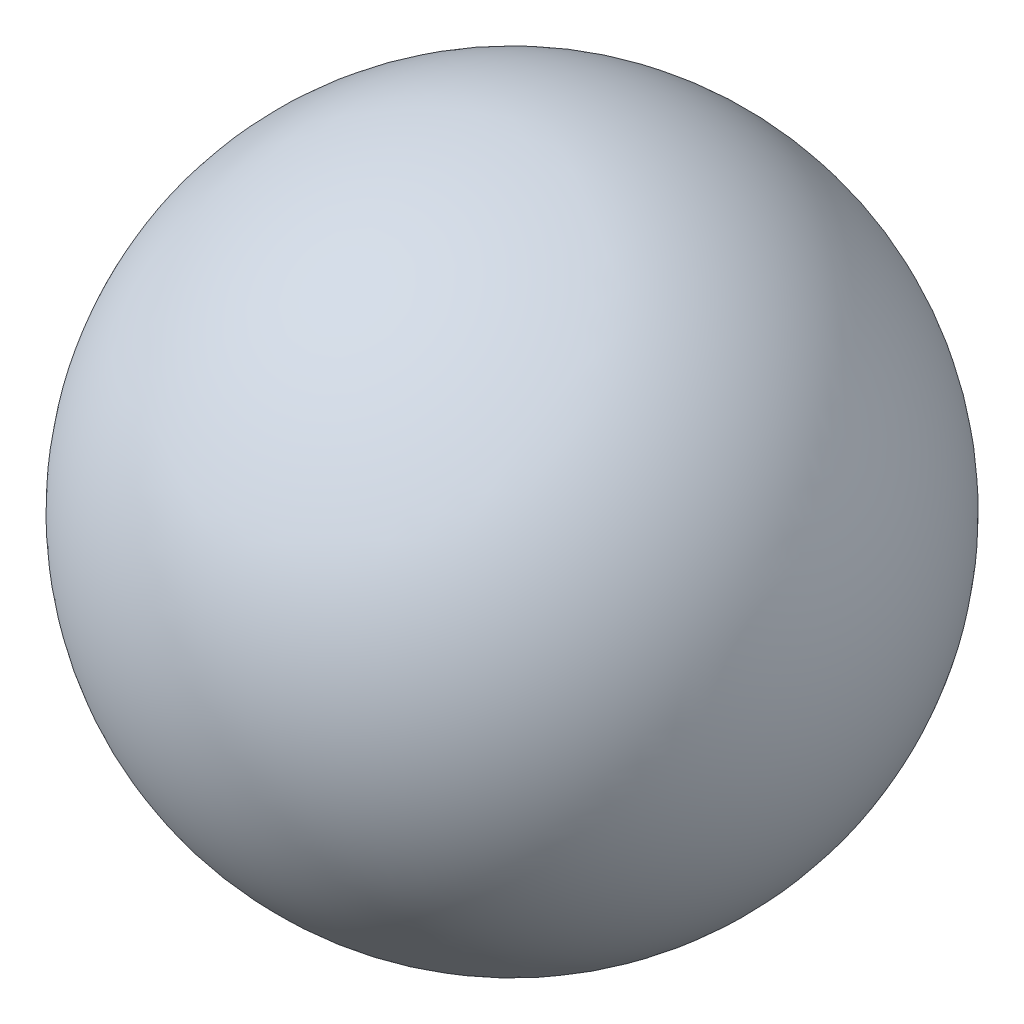
SolidWorks part; units mm, degrees
ref_plane "Alzado" through (0, 0, 0) normal (0, 0, 1) x (1, 0, 0)
ref_plane "Planta" through (0, 0, 0) normal (0, 1, 0) x (1, 0, 0)
ref_plane "Vista lateral" through (0, 0, 0) normal (1, 0, 0) x (0, 0, -1)
ref_plane "Plano1" through (0, 0, 0) normal (0, 0, 1) x (1, 0, 0)
sketch "Croquis1" plane through (0, 0, 0) normal (0, 0, 1) x (1, 0, 0)
  line L0 (10.572, 15) -> (3.428, 15)
  line L1 (50, 15) -> (-50, 15) construction
  arc A0 (3.428, 15) -> (10.572, 15) centre (7, 15) cw
revolve "Revolución1" add sketch "Croquis1" angle 360 about L1
